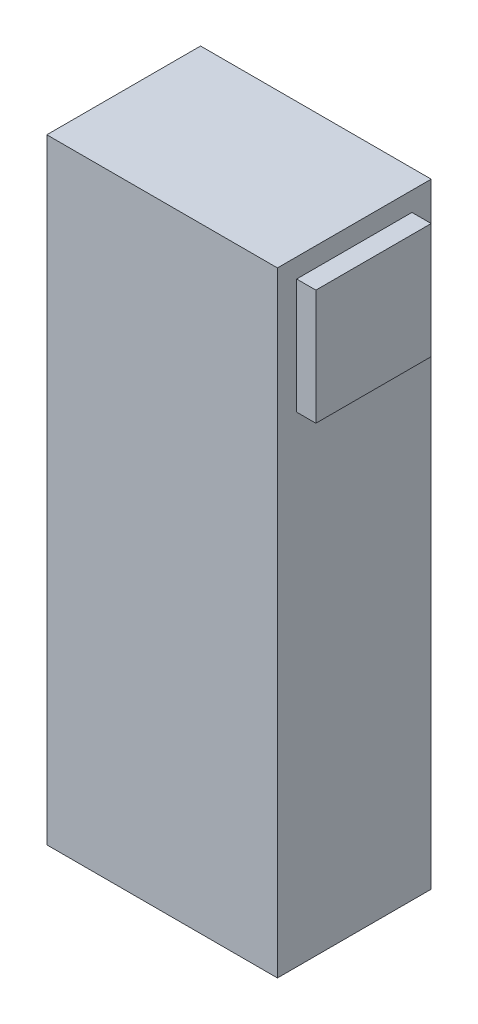
SolidWorks part; units mm, degrees
ref_plane "Front Plane" through (0, 0, 0) normal (0, 0, 1) x (1, 0, 0)
ref_plane "Top Plane" through (0, 0, 0) normal (0, 1, 0) x (1, 0, 0)
ref_plane "Right Plane" through (0, 0, 0) normal (1, 0, 0) x (0, 0, -1)
sketch "Sketch1" plane through (0, 0, 0) normal (0, 1, 0) x (1, 0, 0)
  line L1 (0, 0) -> (38.1, 0)
  line L2 (0, 0) -> (0, 25.4)
  line L3 (0, 25.4) -> (38.1, 25.4)
  line L4 (38.1, 0) -> (38.1, 25.4)
  dimension "D1" = 25.4
  dimension "D2" = 38.1
extrude "Boss-Extrude1" add sketch "Sketch1" along normal blind 101.6
sketch "Sketch2" plane through (38.1, 0, 0) normal (1, 0, 0) x (0, 0, -1)
  line L1 (3.175, 98.425) -> (22.225, 98.425)
  line L2 (3.175, 98.425) -> (3.175, 79.375)
  line L3 (3.175, 79.375) -> (22.225, 79.375)
  line L4 (0, 0) -> (25.4, 0)
  line L5 (25.4, 0) -> (25.4, 101.6)
  line L6 (25.4, 101.6) -> (0, 101.6)
  line L7 (0, 101.6) -> (0, 0)
  line L8 (0, 0) -> (25.4, 0)
  line L9 (25.4, 0) -> (25.4, 101.6)
  line L10 (25.4, 101.6) -> (0, 101.6)
  line L11 (0, 101.6) -> (0, 0)
  line L12 (22.225, 98.425) -> (22.225, 79.375)
  dimension "D2" = 3.175
  dimension "D3" = 3.175
  dimension "D4" = 3.175
  dimension "D1" = 0
extrude "Boss-Extrude2" add sketch "Sketch2" along normal blind 3.175 contours L12 L1 L2 L3
